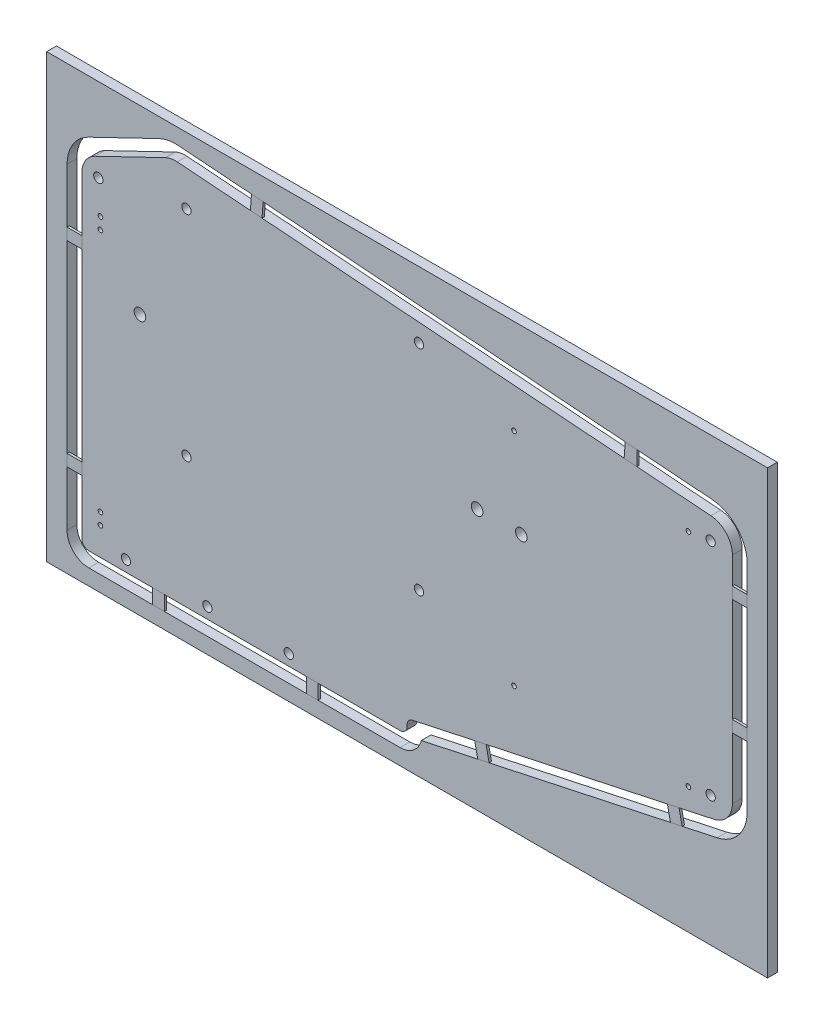
SolidWorks part; units mm, degrees
ref_plane "Front Plane" through (0, 0, 0) normal (0, 0, 1) x (1, 0, 0)
ref_plane "Top Plane" through (0, 0, 0) normal (0, 1, 0) x (1, 0, 0)
ref_plane "Right Plane" through (0, 0, 0) normal (1, 0, 0) x (0, 0, -1)
sketch "Sketch1" plane through (0, 0, 0) normal (0, 0, 1) x (1, 0, 0)
  line L0 (0, 0) -> (0, 145.5572)
  line L1 (38.3294, 164.0519) -> (279.7746, 146.1441)
  line L2 (279.7746, 146.1441) -> (279.7746, 36.1441)
  line L3 (279.7746, 36.1441) -> (139.7746, 5.9958)
  line L4 (139.7746, 5.9958) -> (140, 0)
  line L5 (140, 0) -> (0, 0)
  line L6 (0, 145.5572) -> (38.3294, 164.0519)
  line L7 (45, 148.3671) -> (45, 163.5571) construction
  line L8 (45, 148.3671) -> (45, 56.3671) construction
  line L9 (45, 148.3671) -> (155.3558, 148.3671) construction
  line L10 (45, 56.3671) -> (164.8158, 56.3671) construction
  circle A10 centre (45, 148.3671) radius 2
  circle A11 centre (45, 56.3671) radius 2
  circle A12 centre (145, 148.3671) radius 2
  circle A13 centre (145, 56.3671) radius 2
  dimension "D11" = 4
  dimension "D12" = 15.19
  dimension "D13" = 92
  dimension "D14" = 4
  dimension "D17" = 45
  dimension "D18" = 4
  dimension "D19" = 4
  dimension "D20" = 100
  dimension "D21" = 100
  dimension "D1" = 6
  dimension "D2" = 140
  dimension "D3" = 145.5572
  dimension "D4" = 100
  dimension "D5" = 150
  dimension "D6" = 110
  dimension "D7" = 140
  dimension "D8" = 241.4452
  dimension "D9" = 18.4947
extrude "Boss-Extrude1" add sketch "Sketch1" along normal blind 4.2
sketch "Sketch3" plane through (0, 0, 4.2) normal (0, 0, 1) x (1, 0, 0)
  line L0 (0, 0) -> (140, 0) construction
  line L1 (25, 99.0519) -> (189, 99.0519) construction
  line L2 (279.7746, 146.1441) -> (38.3294, 164.0519) construction
  line L3 (0, 145.5572) -> (0, 0) construction
  line L6 (279.7746, 36.1441) -> (279.7746, 146.1441) construction
  line L7 (139.7746, 5.9958) -> (279.7746, 36.1441) construction
  line L8 (38.3294, 164.0519) -> (0, 145.5572) construction
  circle A0 centre (7.0984, 141.0064) radius 2
  circle A1 centre (19, 4.76) radius 2
  circle A2 centre (54, 4.76) radius 2
  circle A3 centre (89, 4.76) radius 2
  circle A4 centre (270.4246, 137.4619) radius 2
  circle A5 centre (270.4246, 42.672) radius 2
  circle A7 centre (7.0984, 141.0064) radius 6.35 construction
  circle A8 centre (270.4246, 137.4619) radius 6.35 construction
  circle A9 centre (270.4246, 42.672) radius 6.35 construction
  circle A10 centre (25, 99.0519) radius 2.5
  circle A11 centre (189, 99.0519) radius 2.5
  circle A12 centre (170, 99.0519) radius 2.5
  circle A13 centre (8, 12.025) radius 1
  circle A14 centre (8, 17.025) radius 1
  circle A15 centre (8, 127.025) radius 1
  circle A16 centre (8, 122.025) radius 1
  circle A17 centre (185.863, 136.1441) radius 1
  circle A18 centre (260.863, 136.1441) radius 1
  circle A19 centre (185.863, 41.1441) radius 1
  circle A20 centre (260.863, 41.1441) radius 1
  point P52 (0, 0)
  point P54 (0, 0)
  point P55 (0, 0)
  point P56 (0, 0)
  dimension "D1" = 4
  dimension "D2" = 4
  dimension "D3" = 4
  dimension "D4" = 5
  dimension "D5" = 5
  dimension "D7" = 35
  dimension "D8" = 35
  dimension "D9" = 4.76
  dimension "D10" = 7.0984
  dimension "D11" = 7.1834
  dimension "D12" = 12.7
  dimension "D13" = 164
  dimension "4" = 4
  dimension "D14" = 9.35
  dimension "D15" = 9.35
  dimension "D16" = 12.7
  dimension "D17" = 12.7
  dimension "D18" = 9.35
  dimension "D19" = 8.35
  dimension "D20" = 25
  dimension "D21" = 65
  dimension "D22" = 5
  dimension "D23" = 145
  dimension "D24" = 2
  dimension "D25" = 2
  dimension "D26" = 8
  dimension "D29" = 2
  dimension "D30" = 2
  dimension "D32" = 8
  dimension "D33" = 105
  dimension "D34" = 75
  dimension "D35" = 2
  dimension "D36" = 2
  dimension "D37" = 10
  dimension "D38" = 2
  dimension "D39" = 2
  dimension "D40" = 95
  dimension "D6" = 19
  dimension "D27" = 5
  dimension "D28" = 12.025
  dimension "D31" = 5
extrude "Cut-Extrude1" cut sketch "Sketch3" against normal through all
fillet "Fillet1" radius 10 4 edges at (0, 145.5572, 2.1) (38.3294, 164.0519, 2.1) (279.7746, 36.1441, 2.1) (279.7746, 146.1441, 2.1)
fillet "Fillet2" radius 3 1 edges at (139.7746, 5.9958, 2.1)
fillet "Fillet3" radius 3 2 edges at (0, 0, 2.1) (140, 0, 2.1)
sketch "Sketch5" plane through (0, 0, 4.2) normal (0, 0, 1) x (1, 0, 0)
  line L0 (38.3953, 163.7053) -> (38.3953, 0) construction
  line L1 (3, 0) -> (136.8851, 0) construction
  line L2 (0, 0) -> (279.7746, 0) construction
  line L3 (0, 0) -> (0, 180.3037) construction
  line L4 (279.7746, 0) -> (279.7746, 180.3037) construction
  line L5 (279.7746, 44.2199) -> (279.7746, 136.8583) construction
  line L6 (0, 81.8527) -> (279.7746, 81.8527) construction
  line L19 (-15.1127, 176.8527) -> (294.8873, 176.8527)
  line L20 (-15.1127, 176.8527) -> (-15.1127, -13.1473)
  line L21 (-15.1127, -13.1473) -> (294.8873, -13.1473)
  line L22 (294.8873, 176.8527) -> (294.8873, -13.1473)
  line L23 (-15.1127, 176.8527) -> (294.8873, -13.1473) construction
  line L24 (-15.1127, -13.1473) -> (294.8873, 176.8527) construction
  line L25 (-6.35, 139.2791) -> (-6.35, 3)
  line L26 (3, -6.35) -> (136.8851, -6.35)
  line L27 (145.9814, 0.8368) -> (273.2166, 28.2363)
  line L28 (286.1246, 44.2199) -> (286.1246, 136.8583)
  line L29 (270.984, 153.1635) -> (41.4712, 170.1863)
  line L30 (33.1566, 168.6065) -> (2.8947, 154.0045)
  line L31 (-6.35, 139.2791) -> (-6.35, 3)
  line L32 (3, -6.35) -> (136.8851, -6.35)
  line L33 (145.9814, 0.8368) -> (273.2166, 28.2363)
  line L34 (286.1246, 44.2199) -> (286.1246, 136.8583)
  line L35 (270.984, 153.1635) -> (41.4712, 170.1863)
  line L36 (33.1566, 168.6065) -> (2.8947, 154.0045)
  arc A0 (41.0016, 163.8537) -> (35.9162, 162.8874) centre (40.2619, 153.8811) ccw construction
  arc A15 (-6.35, 3) -> (3, -6.35) centre (3, 3) ccw
  arc A16 (136.8851, -6.35) -> (145.9814, 0.8368) centre (136.8851, 3) ccw
  arc A17 (273.2166, 28.2363) -> (286.1246, 44.2199) centre (269.7746, 44.2199) ccw
  arc A18 (286.1246, 136.8583) -> (270.984, 153.1635) centre (269.7746, 136.8583) ccw
  arc A19 (41.4712, 170.1863) -> (33.1566, 168.6065) centre (40.2619, 153.8811) ccw
  arc A20 (2.8947, 154.0045) -> (-6.35, 139.2791) centre (10, 139.2791) ccw
  arc A21 (-6.35, 3) -> (3, -6.35) centre (3, 3) ccw
  arc A22 (136.8851, -6.35) -> (145.9814, 0.8368) centre (136.8851, 3) ccw
  arc A23 (273.2166, 28.2363) -> (286.1246, 44.2199) centre (269.7746, 44.2199) ccw
  arc A24 (286.1246, 136.8583) -> (270.984, 153.1635) centre (269.7746, 136.8583) ccw
  arc A25 (41.4712, 170.1863) -> (33.1566, 168.6065) centre (40.2619, 153.8811) ccw
  arc A26 (2.8947, 154.0045) -> (-6.35, 139.2791) centre (10, 139.2791) ccw
  point P14 (38.3953, 81.8527)
  point P17 (139.8873, 81.8527)
  point P18 (139.8873, 81.8527)
  dimension "D1" = 6.35
  dimension "D2" = 310
  dimension "D3" = 190
extrude "Boss-Extrude2" add sketch "Sketch5" against normal up to surface (4.2 mm away) separate body up to face at (191.5, 99.0519, 0)
sketch "Sketch6" plane through (0, 0, 4.2) normal (0, 0, 1) x (1, 0, 0)
  line L0 (0, 115.8718) -> (-6.35, 115.8718)
  line L1 (0, 139.2791) -> (0, 3) construction
  line L2 (-6.35, 139.2791) -> (-6.35, 3) construction
  line L3 (-6.35, 115.8718) -> (-6.35, 110.8718)
  line L4 (-6.35, 110.8718) -> (0, 110.8718)
  line L5 (0, 110.8718) -> (0, 115.8718)
  line L6 (72.9633, 167.8506) -> (72.4937, 161.5179)
  line L7 (270.984, 153.1635) -> (41.4712, 170.1863) construction
  line L8 (270.5143, 146.8309) -> (41.0016, 163.8537) construction
  line L9 (72.4937, 161.5179) -> (77.4937, 161.1471)
  line L10 (77.4937, 161.1471) -> (77.9633, 167.4797)
  line L11 (77.9633, 167.4797) -> (72.9633, 167.8506)
  line L12 (-6.35, 31.6124) -> (0, 31.6124)
  line L13 (0, 31.6124) -> (0, 26.6124)
  line L14 (0, 26.6124) -> (-6.35, 26.6124)
  line L15 (-6.35, 26.6124) -> (-6.35, 31.6124)
  line L16 (30.4656, 0) -> (30.4656, -6.35)
  line L17 (3, 0) -> (136.8851, 0) construction
  line L18 (3, -6.35) -> (136.8851, -6.35) construction
  line L19 (30.4656, -6.35) -> (35.4656, -6.35)
  line L20 (35.4656, -6.35) -> (35.4656, 0)
  line L21 (35.4656, 0) -> (30.4656, 0)
  line L22 (96.5483, 0) -> (96.5483, -6.35)
  line L23 (96.5483, -6.35) -> (101.5483, -6.35)
  line L24 (101.5483, -6.35) -> (101.5483, 0)
  line L25 (101.5483, 0) -> (96.5483, 0)
  line L26 (168.9533, 12.2793) -> (170.2901, 6.0716)
  line L27 (142.2355, 6.5257) -> (271.8798, 34.444) construction
  line L28 (145.9814, 0.8368) -> (273.2166, 28.2363) construction
  line L29 (170.2901, 6.0716) -> (175.178, 7.1242)
  line L30 (175.178, 7.1242) -> (173.8412, 13.3318)
  line L31 (173.8412, 13.3318) -> (168.9533, 12.2793)
  line L32 (251.832, 30.1268) -> (253.1688, 23.9191)
  line L33 (253.1688, 23.9191) -> (258.1688, 24.9958)
  line L34 (258.1688, 24.9958) -> (256.832, 31.2035)
  line L35 (256.832, 31.2035) -> (251.832, 30.1268)
  line L36 (279.7746, 120.2781) -> (286.1246, 120.2781)
  line L37 (279.7746, 44.2199) -> (279.7746, 136.8583) construction
  line L38 (286.1246, 44.2199) -> (286.1246, 136.8583) construction
  line L39 (286.1246, 120.2781) -> (286.1246, 125.2781)
  line L40 (286.1246, 125.2781) -> (279.7746, 125.2781)
  line L41 (279.7746, 125.2781) -> (279.7746, 120.2781)
  line L42 (279.7746, 75.5682) -> (279.7746, 70.5682)
  line L43 (279.7746, 70.5682) -> (286.1246, 70.5682)
  line L44 (286.1246, 70.5682) -> (286.1246, 75.5682)
  line L45 (286.1246, 75.5682) -> (279.7746, 75.5682)
  line L46 (233.6791, 155.9304) -> (233.2094, 149.5978)
  line L47 (233.2094, 149.5978) -> (238.6791, 149.1921)
  line L48 (238.6791, 149.1921) -> (238.6791, 155.5596)
  line L49 (238.6791, 155.5596) -> (233.6791, 155.9304)
  dimension "D1" = 5
  dimension "D2" = 5
  dimension "D3" = 5
  dimension "D4" = 5
  dimension "D5" = 5
  dimension "D6" = 5
  dimension "D7" = 5
  dimension "D8" = 5
  dimension "D9" = 5
  dimension "D10" = 5
extrude "Boss-Extrude3" add sketch "Sketch6" against normal blind 1 separate body
